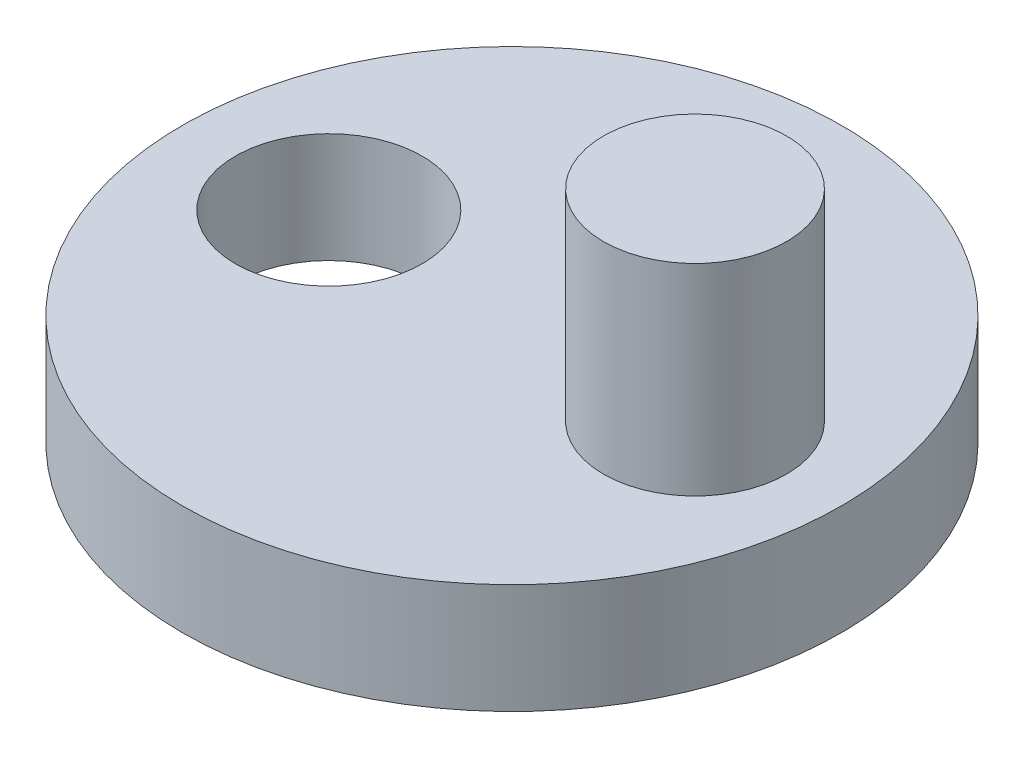
SolidWorks part; units mm, degrees
ref_plane "Front Plane" through (0, 0, 0) normal (0, 0, 1) x (1, 0, 0)
ref_plane "Top Plane" through (0, 0, 0) normal (0, 1, 0) x (1, 0, 0)
ref_plane "Right Plane" through (0, 0, 0) normal (1, 0, 0) x (0, 0, -1)
sketch "Sketch1" plane through (0, 0, 0) normal (0, 1, 0) x (1, 0, 0)
  circle A0 centre (0, 0) radius 9
  circle A1 centre (5, 0) radius 2.3 construction
  circle A2 centre (-5, -0.0008) radius 2.55
  dimension "D1" = 18
  dimension "D4" = 5.1
  dimension "D5" = 4.6
  dimension "D2" = 5
  dimension "D3" = 5
extrude "Boss-Extrude1" add sketch "Sketch1" along normal blind 3
sketch "Sketch2" plane through (0, 3, 0) normal (0, 1, 0) x (1, 0, 0)
  circle A0 centre (5, 0) radius 2.5
  dimension "D1" = 5
extrude "Boss-Extrude2" add sketch "Sketch2" along normal blind 5.5
